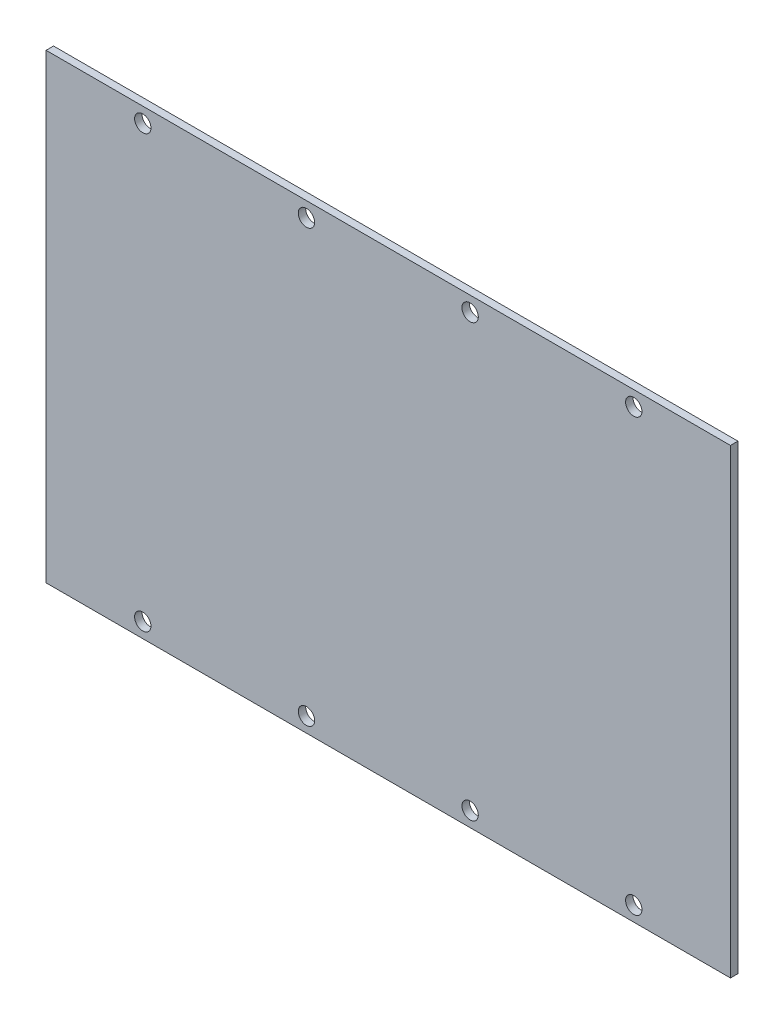
SolidWorks part; units mm, degrees
material "6061-T6 (SS)"
ref_plane "Front Plane" through (0, 0, 0) normal (0, 0, 1) x (1, 0, 0)
ref_plane "Top Plane" through (0, 0, 0) normal (0, 1, 0) x (1, 0, 0)
ref_plane "Right Plane" through (0, 0, 0) normal (1, 0, 0) x (0, 0, -1)
sketch "Sketch1" plane through (0, 0, 0) normal (0, 0, 1) x (1, 0, 0)
  line L0 (0, -62) -> (92, -62)
  line L1 (0, 0) -> (92, 0)
  line L2 (0, 0) -> (0, -62)
  line L4 (92, 0) -> (92, -62)
  dimension "D1" = 92
  dimension "D2" = 62
extrude "Boss-Extrude1" add sketch "Sketch1" against normal blind 1
hole_wizard "Ø2.2 (2.2) Diameter Hole2" positions "Sketch5" profile "Sketch4" hole size "Ø2.2" standard "ANSI Metric" end condition through all
sketch "Sketch5" plane through (0, 0, -1) normal (0, 0, -1) x (-1, 0, 0)
  line L2 (0, 0) -> (0, -62) construction
  line L3 (0, -62) -> (-92, -62) construction
  line L4 (-92, 0) -> (0, 0) construction
  point P0 (-79, -2)
  point P2 (-57, -2)
  point P4 (-35, -2)
  point P6 (-13, -2)
  point P8 (-13, -60)
  point P10 (-35, -60)
  point P12 (-57, -60)
  point P14 (-79, -60)
  dimension "D2" = 13
  dimension "D3" = 22
  dimension "D4" = 22
  dimension "D5" = 22
  dimension "D6" = 13
  dimension "D7" = 22
  dimension "D8" = 22
  dimension "D9" = 22
  dimension "D10" = 2
  dimension "D11" = 2
sketch "Sketch4" plane through (79, -2, -1) normal (1, 0, 0) x (0, 1, 0)
  line L0 (0, 0) -> (0, 1)
  line L1 (0, 1) -> (1.1, 1)
  line L2 (1.1, 1) -> (1.1, 0)
  line L5 (1.1, 0) -> (0, 0)
  line L11 (0, -6.35) -> (0, 107.95) construction
  dimension "Thru Hole Dia." = 2.2
  dimension "Thru Hole Depth" = 1
